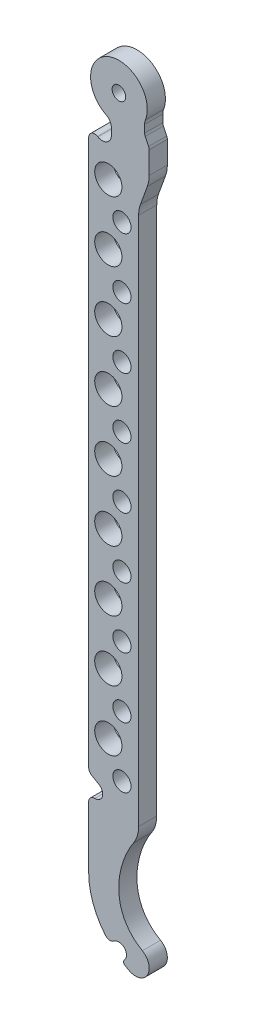
SolidWorks part; units mm, degrees
material "Сплав 2024"
ref_plane "Спереди" through (0, 0, 0) normal (0, 0, 1) x (1, 0, 0)
ref_plane "Сверху" through (0, 0, 0) normal (0, 1, 0) x (1, 0, 0)
ref_plane "Справа" through (0, 0, 0) normal (1, 0, 0) x (0, 0, -1)
sketch "Эскиз1" plane through (0, 0, 0) normal (0, 0, 1) x (1, 0, 0)
  line L0 (0, 19.9837) -> (0, -254.7255) construction
  line L1 (-29.97, -250) -> (36.7046, -250) construction
  line L2 (10, 23.4276) -> (10, -280.6569) construction
  line L3 (5.5, -245.5) -> (2.9019, -250) construction
  line L4 (6.5, -30) -> (6.5, -210)
  line L5 (6.5, -30) -> (10, -20.3838)
  line L6 (10, -237.7058) -> (5.5, -245.5) construction
  line L7 (-1.25, -243.3349) -> (-3.342, -244.5428)
  line L8 (-10, -227.9756) -> (-10, 0)
  line L9 (1.25, -247.6651) -> (0.749, -247.9543)
  line L10 (10, -20.3838) -> (10, 0)
  arc A0 (10, 0) -> (-10, 0) centre (0, 0) ccw
  arc A1 (3.25, -249.3971) -> (7.75, -241.6029) centre (5.5, -245.5) ccw
  arc A2 (1.25, -247.6651) -> (-1.25, -243.3349) centre (0, -245.5) ccw
  circle A3 centre (11, -226) radius 11 construction
  arc A4 (-10, -227.9756) -> (-3.342, -244.5428) centre (13.9413, -227.9756) ccw
  arc A5 (0.749, -247.9543) -> (3.25, -249.3971) centre (13.9413, -227.9756) ccw
  spline S0 degree 3 poles (7.75, -241.6029) (-4.554, -234.4992) (-0.2099, -217.8442) (6.5, -210) knots 0 0 0 0 1 1 1 1
  dimension "D1" = 20
  dimension "D3" = 60
  dimension "D4" = 9
  dimension "D5" = 22
  dimension "D10" = 5
  dimension "D2" = 250
  dimension "D6" = 40
  dimension "D7" = 3.5
  dimension "D8" = 24
  dimension "D9" = 30
  dimension "D11" = 30
  dimension "D12" = 20
extrude "Бобышка-Вытянуть1" add sketch "Эскиз1" along normal blind 6
sketch "Эскиз2" plane through (0, 0, 6) normal (0, 0, 1) x (1, 0, 0)
  line L0 (-6.5942, -201.1783) -> (-10, -199.212)
  line L2 (-10, 0) -> (-10, -227.9756) construction
  line L3 (-10, -199.212) -> (-10, -204.9855)
  line L4 (-10, -204.9855) -> (-9.0942, -205.5085)
  arc A0 (-9.0942, -205.5085) -> (-6.5942, -201.1783) centre (-7.8442, -203.3434) ccw
  dimension "D1" = 5
  dimension "D2" = 60
extrude "Вырез-Вытянуть1" cut sketch "Эскиз2" against normal through all
hole_wizard "Отверстие с зазором M41" positions "Эскиз5" profile "Эскиз4" hole size "M4" standard "Ansi Metric" end condition through all
sketch "Эскиз5" plane through (0, 0, 6) normal (0, 0, 1) x (1, 0, 0)
  point P0 (0, 0)
sketch "Эскиз4" plane through (0, 0, 6) normal (1, 0, 0) x (0, -1, 0)
  line L0 (0, 0) -> (0, 6)
  line L1 (0, 6) -> (2.25, 6)
  line L2 (2.25, 6) -> (2.25, 0)
  line L5 (2.25, 0) -> (0, 0)
  line L11 (0, -6.35) -> (0, 107.95) construction
  dimension "Диаметр сквозного отверстия" = 4.5
  dimension "Глубина сквозного отверстия" = 6
sketch "Эскиз6" plane through (0, 0, 6) normal (0, 0, 1) x (1, 0, 0)
  line L0 (5.9995, 10.7781) -> (-10.4551, -18.7828) construction
  line L1 (-11.3191, 4.2819) -> (11.3554, -4.2956) construction
  line L2 (-10, 0) -> (-10, -199.212) construction
  line L3 (-2.5, -6.4717) -> (-2.5, -19.6446) construction
  line L4 (8.5, 0) -> (8.5, -15.9886) construction
  line L5 (10, -20.3838) -> (10, 0) construction
  line L6 (-16.2507, -12) -> (0.9843, -12) construction
  arc A1 (8.7587, -3.3134) -> (-4.5545, -8.1823) centre (0, 0) ccw
  arc A2 (16.2413, -6.1439) -> (-8.4455, -15.1724) centre (0, 0) ccw
  arc A3 (-8.4455, -15.1724) -> (-4.5545, -8.1823) centre (-6.5, -11.6773) ccw
  arc A4 (8.7587, -3.3134) -> (16.2413, -6.1439) centre (12.5, -4.7287) ccw
  circle A6 centre (0, 0) radius 9.3645 construction
  circle A7 centre (0, 0) radius 17.3645 construction
  point P8 (7.1723, 2.1928)
  point P17 (3.3471, 1.0233)
  dimension "D4" = 7.5
  dimension "D5" = 1.5
  dimension "D1" = 8
extrude "Вырез-Вытянуть2" cut sketch "Эскиз6" against normal through all
sketch "Эскиз10" [suppressed] plane through (0, 0, 6) normal (0, 0, 1) x (1, 0, 0)
  line L0 (-10, -14.196) -> (-10, -15.696) construction
  line L1 (-10, -14.196) -> (-10, -199.212) construction
  line L2 (-10, -15.696) -> (-6.6008, -15.4382)
  line L3 (-2.5, -11.6773) -> (-16.4533, -11.6773) construction
  line L4 (-10, -15.696) -> (-11.1684, -12.4935)
  line L5 (8.5, -4.7287) -> (13.0312, -4.7287) construction
  line L6 (-0.9784, -9.3133) -> (-4.6006, -7.1076)
  arc A0 (-6.6008, -15.4382) -> (-3.5631, -7.978) centre (-6.941, -10.9511) ccw
  arc A1 (-8.4455, -15.1724) -> (-4.5545, -8.1823) centre (-6.5, -11.6773) ccw construction
  circle A2 centre (13, -4.7287) radius 4.5
  arc A3 (8.7587, -3.3134) -> (10, -7.8512) centre (12.5, -4.7287) ccw construction
  arc A4 (-0.9784, -9.3133) -> (-3.5631, -7.978) centre (-0.5605, -5.3351) ccw
  arc A5 (8.7587, -3.3134) -> (-4.5545, -8.1823) centre (0, 0) ccw construction
  arc A6 (-4.6006, -7.1076) -> (-11.1684, -12.4935) centre (-6.941, -10.9511) ccw
  dimension "D2" = 9
  dimension "D3" = 9
  dimension "D4" = 8
  dimension "D1" = 1.5
extrude "Вырез-Вытянуть5" [suppressed] cut sketch "Эскиз10" against normal blind 10
sketch "Эскиз9" plane through (0, 0, 6) normal (0, 0, 1) x (1, 0, 0)
  line L0 (1, -15.9204) -> (1, -196.7254) construction
  line L1 (-3.5, -15.9204) -> (-3.5, -196.7254) construction
  line L5 (6.5, -210) -> (6.5, -30) construction
  line L6 (-10, -204.9855) -> (-10, -227.9756) construction
  circle A0 centre (1, -36.4645) radius 3
  circle A1 centre (1, -56.4645) radius 3
  circle A2 centre (1, -76.4645) radius 3
  circle A3 centre (1, -96.4645) radius 3
  circle A4 centre (1, -116.4645) radius 3
  circle A5 centre (1, -136.4645) radius 3
  circle A6 centre (1, -156.4645) radius 3
  circle A7 centre (1, -176.4645) radius 3
  circle A8 centre (1, -196.4645) radius 3
  circle A9 centre (-3.5, -26.4645) radius 4.5
  circle A10 centre (-3.5, -46.4645) radius 4.5
  circle A11 centre (-3.5, -66.4645) radius 4.5
  circle A12 centre (-3.5, -86.4645) radius 4.5
  circle A13 centre (-3.5, -106.4645) radius 4.5
  circle A14 centre (-3.5, -126.4645) radius 4.5
  circle A15 centre (-3.5, -146.4645) radius 4.5
  circle A16 centre (-3.5, -166.4645) radius 4.5
  circle A18 centre (-3.5, -186.4645) radius 4.5
  dimension "D3" = 6
  dimension "D5" = 9
  dimension "D1" = 5.5
  dimension "D2" = 6.5
  dimension "D6" = 10
  dimension "D4" = 9
  dimension "D7" = 9
extrude "Вырез-Вытянуть4" cut sketch "Эскиз9" against normal through all
sketch "Эскиз11" plane through (0, 0, 6) normal (0, 0, 1) x (1, 0, 0)
  line L0 (-2.5, 7.9999) -> (-2.5, -26.6811) construction
  line L1 (10, -20.3838) -> (10, -7.8512) construction
  line L2 (-2.5, -9.3259) -> (-2.5, -18.4818)
  line L3 (-2.5, -18.4818) -> (-10, -14.307)
  line L4 (-10, -14.196) -> (-10, -199.212) construction
  line L5 (-10, -14.307) -> (-10, -5.1512)
  line L6 (-10, -5.1512) -> (-2.5, -9.3259)
  line L7 (8.5, -0.5673) -> (8.5, -26.1424) construction
  line L8 (10, -7.8512) -> (10, -10.8042)
  line L9 (5.9995, 10.7781) -> (-10.4551, -18.7828) construction
  line L10 (10, -20.3838) -> (10, -7.8512) construction
  line L11 (10, -10.8042) -> (8.5, -7.6817)
  line L12 (8.5, -7.6817) -> (8.5, -4.7287)
  line L13 (8.5, -4.7287) -> (10, -7.8512)
  arc A1 (8.7587, -3.3134) -> (10, -7.8512) centre (12.5, -4.7287) ccw construction
  dimension "D1" = 0
  dimension "D2" = 0
  dimension "D3" = 7.5
  dimension "D4" = 1.5
extrude "Вырез-Вытянуть6" cut sketch "Эскиз11" against normal through all
fillet "Скругление4" radius 2 6 edges at (-3.342, -244.5428, 3) (-10, -204.9855, 3) (-10, -199.212, 3) (8.5, -7.6817, 3) (-10, -14.307, 3) (10, -10.8042, 3)
fillet "Скругление5" radius 10 3 edges at (6.5, -210, 3) (6.5, -30, 3) (10, -20.3838, 3)
fillet "Скругление6" radius 1 1 edges at (0.749, -247.9543, 3)
fillet "Скругление7" radius 3 2 edges at (-2.5, -18.4818, 3) (-2.5, -9.3259, 3)
